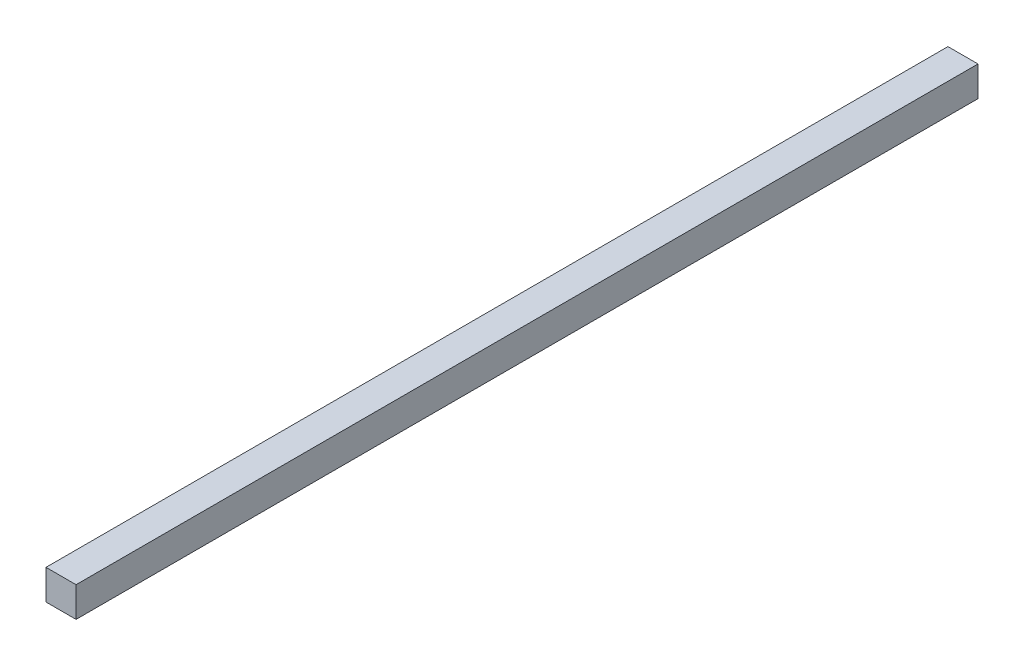
SolidWorks part; units mm, degrees
ref_plane "Front Plane" through (0, 0, 0) normal (0, 0, 1) x (1, 0, 0)
ref_plane "Top Plane" through (0, 0, 0) normal (0, 1, 0) x (1, 0, 0)
ref_plane "Right Plane" through (0, 0, 0) normal (1, 0, 0) x (0, 0, -1)
sketch "Sketch1" plane through (0, 0, 0) normal (0, 0, 1) x (1, 0, 0)
  line L1 (37.0609, 22.86) -> (11.6609, 22.86)
  line L2 (37.0609, 22.86) -> (37.0609, -2.54)
  line L3 (37.0609, -2.54) -> (11.6609, -2.54)
  line L4 (11.6609, 22.86) -> (11.6609, -2.54)
  line L5 (37.0609, 22.86) -> (11.6609, -2.54) construction
  line L6 (37.0609, -2.54) -> (11.6609, 22.86) construction
  point P0 (24.3609, 10.16)
  dimension "D1" = 25.4
  dimension "D2" = 25.4
extrude "Boss-Extrude1" add sketch "Sketch1" along normal blind 762
